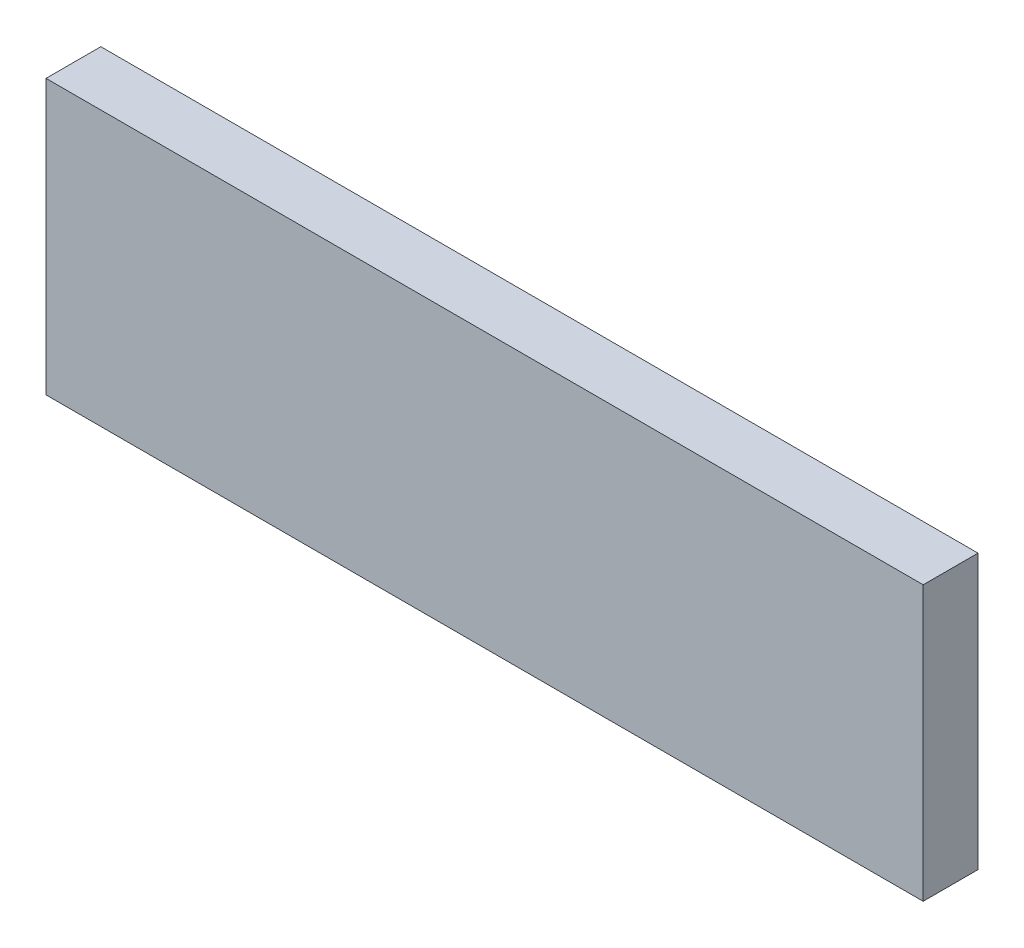
SolidWorks part; units mm, degrees
ref_plane "正面" through (0, 0, 0) normal (0, 0, 1) x (1, 0, 0)
ref_plane "平面" through (0, 0, 0) normal (0, 1, 0) x (1, 0, 0)
ref_plane "右側面" through (0, 0, 0) normal (1, 0, 0) x (0, 0, -1)
sketch "ｽｹｯﾁ1" plane through (0, 0, 0) normal (0, 0, 1) x (1, 0, 0)
  line L1 (-67.7288, 6.0542) -> (92.2712, 6.0542)
  line L2 (-67.7288, 6.0542) -> (-67.7288, -43.9458)
  line L3 (-67.7288, -43.9458) -> (92.2712, -43.9458)
  line L4 (92.2712, 6.0542) -> (92.2712, -43.9458)
  dimension "D1" = 160
  dimension "D2" = 50
extrude "ﾎﾞｽ - 押し出し1" add sketch "ｽｹｯﾁ1" along normal blind 10
